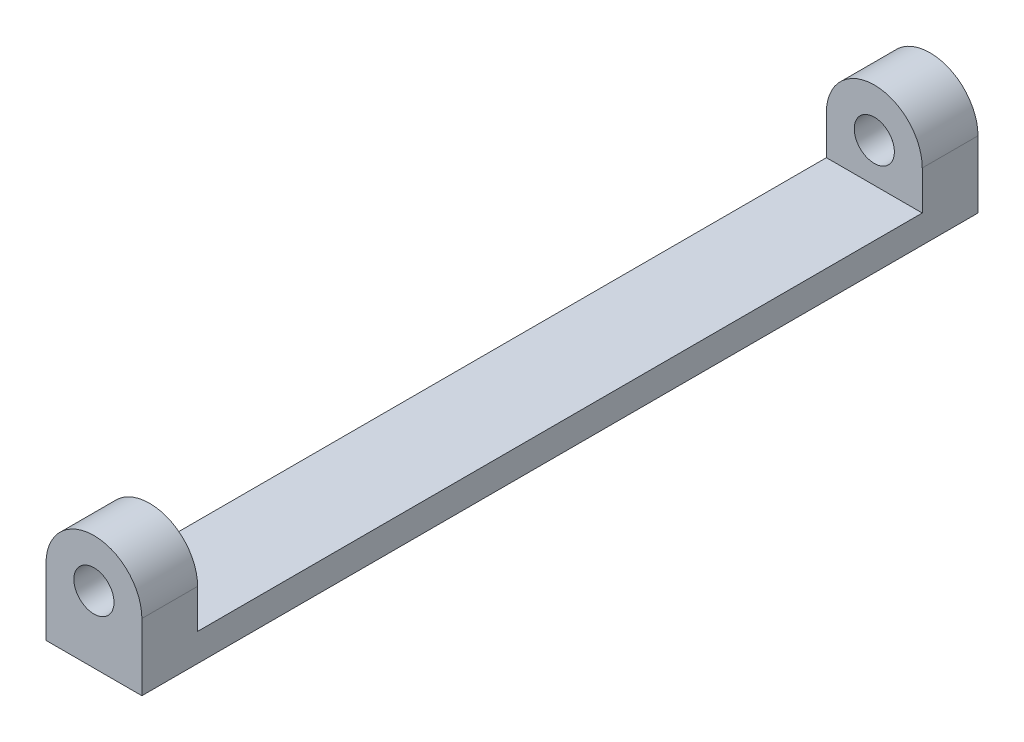
SolidWorks part; units mm, degrees
ref_plane "Front Plane" through (0, 0, 0) normal (0, 0, 1) x (1, 0, 0)
ref_plane "Top Plane" through (0, 0, 0) normal (0, 1, 0) x (1, 0, 0)
ref_plane "Right Plane" through (0, 0, 0) normal (1, 0, 0) x (0, 0, -1)
sketch "Sketch1" plane through (0, 0, 0) normal (0, 0, 1) x (1, 0, 0)
  line L1 (0, 0) -> (10.922, 0)
  line L2 (0, 0) -> (0, 7.62)
  line L4 (10.922, 0) -> (10.922, 7.62)
  arc A0 (10.922, 7.62) -> (0, 7.62) centre (5.461, 7.62) ccw
  circle A2 centre (5.461, 7.62) radius 2.286
  dimension "D1" = 4.572
  dimension "D2" = 3.175
  dimension "D3" = 7.62
  dimension "D4" = 7.62
extrude "Boss-Extrude1" add sketch "Sketch1" along normal blind 95.25
sketch "Sketch2" plane through (10.922, 0, 0) normal (1, 0, 0) x (0, 0, -1)
  line L0 (0, 13.081) -> (-95.25, 13.081) construction
  line L1 (-88.9, 13.081) -> (-6.35, 13.081)
  line L2 (-88.9, 13.081) -> (-88.9, 3.175)
  line L3 (-88.9, 3.175) -> (-6.35, 3.175)
  line L4 (-6.35, 13.081) -> (-6.35, 3.175)
  line L5 (-95.25, 0) -> (0, 0) construction
  line L6 (-95.25, 0) -> (-95.25, 7.62) construction
  line L7 (0, 0) -> (0, 7.62) construction
  dimension "D1" = 3.175
  dimension "D2" = 6.35
  dimension "D3" = 6.35
extrude "Cut-Extrude1" cut sketch "Sketch2" against normal through all
